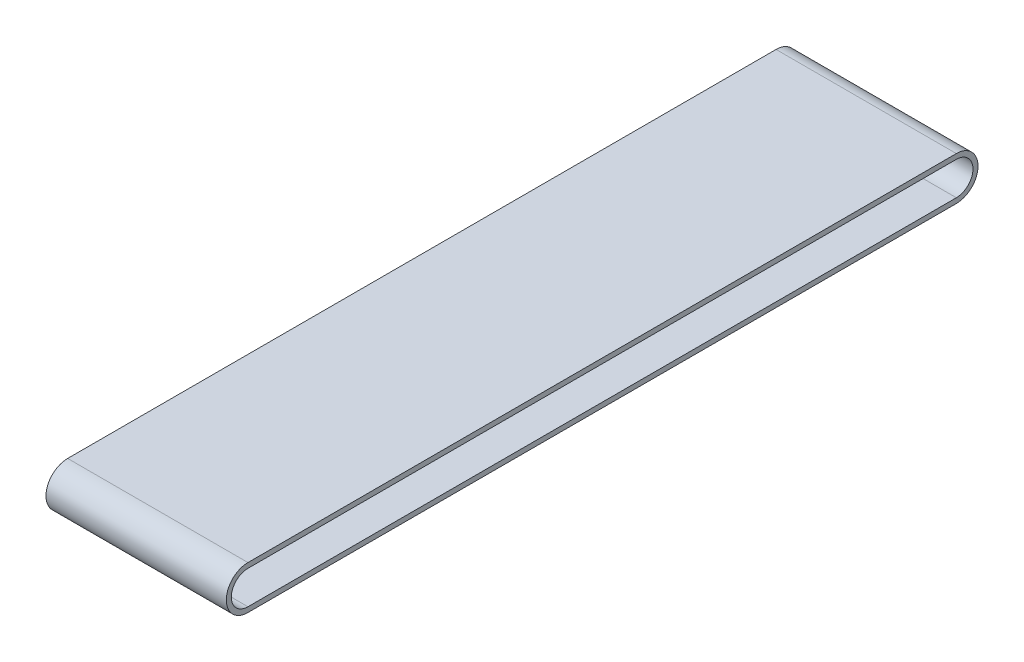
SolidWorks part; units mm, degrees
ref_plane "Front Plane" through (0, 0, 0) normal (0, 0, 1) x (1, 0, 0)
ref_plane "Top Plane" through (0, 0, 0) normal (0, 1, 0) x (1, 0, 0)
ref_plane "Right Plane" through (0, 0, 0) normal (1, 0, 0) x (0, 0, -1)
sketch "Sketch1" plane through (0, 0, 0) normal (1, 0, 0) x (0, 0, -1)
  line L0 (-469.0392, 3.3715) -> (513.2398, 3.3715) construction
  line L3 (-469.0392, 26.4212) -> (513.2398, 26.4212)
  line L6 (-469.0392, -19.6782) -> (513.2398, -19.6782)
  line L7 (513.2398, 3.3715) -> (-469.0392, 3.3715) construction
  line L8 (513.2398, -26.6581) -> (-469.0392, -26.6581)
  line L9 (513.2398, 33.4011) -> (-469.0392, 33.4011)
  arc A4 (-469.0392, 26.4212) -> (-469.0392, -19.6782) centre (-469.0392, 3.3715) ccw
  arc A5 (513.2398, -19.6782) -> (513.2398, 26.4212) centre (513.2398, 3.3715) ccw
  arc A6 (513.2398, -26.6581) -> (513.2398, 33.4011) centre (513.2398, 3.3715) ccw
  arc A7 (-469.0392, 33.4011) -> (-469.0392, -26.6581) centre (-469.0392, 3.3715) ccw
  point P2 (0, 0)
  point P4 (22.1003, 3.3715)
  point P10 (0, 0)
  point P12 (22.1003, 3.3715)
extrude "Boss-Extrude1" add sketch "Sketch1" along normal blind 250
